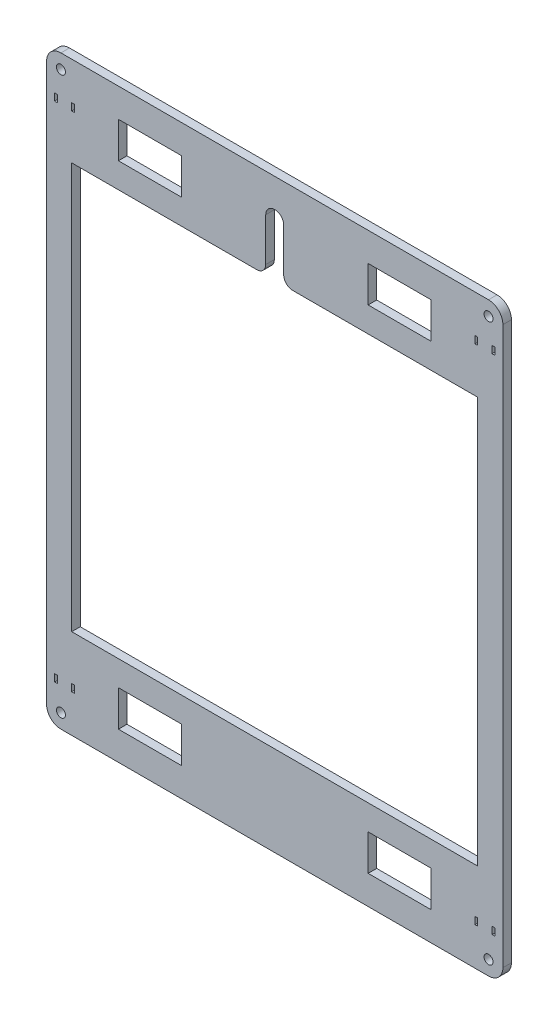
SolidWorks part; units mm, degrees
ref_plane "Front Plane" through (0, 0, 0) normal (0, 0, 1) x (1, 0, 0)
ref_plane "Top Plane" through (0, 0, 0) normal (0, 1, 0) x (1, 0, 0)
ref_plane "Right Plane" through (0, 0, 0) normal (1, 0, 0) x (0, 0, -1)
sketch "Sketch1" plane through (0, 0, 0) normal (0, 0, 1) x (1, 0, 0)
  line L4 (-66.9426, 67.8064) -> (-66.9426, -242.1936)
  line L5 (-58.9426, -250.1936) -> (179.0574, -250.1936)
  line L6 (187.0574, -242.1936) -> (187.0574, 67.8064)
  line L7 (179.0574, 75.8064) -> (-58.9426, 75.8064)
  line L8 (-66.9426, 67.8064) -> (-66.9426, -242.1936)
  line L9 (-58.9426, -250.1936) -> (179.0574, -250.1936)
  line L10 (187.0574, -242.1936) -> (187.0574, 67.8064)
  line L11 (179.0574, 75.8064) -> (-58.9426, 75.8064)
  arc A4 (-66.9426, -242.1936) -> (-58.9426, -250.1936) centre (-58.9426, -242.1936) ccw
  arc A5 (179.0574, -250.1936) -> (187.0574, -242.1936) centre (179.0574, -242.1936) ccw
  arc A6 (187.0574, 67.8064) -> (179.0574, 75.8064) centre (179.0574, 67.8064) ccw
  arc A7 (-58.9426, 75.8064) -> (-66.9426, 67.8064) centre (-58.9426, 67.8064) ccw
  arc A8 (-66.9426, -242.1936) -> (-58.9426, -250.1936) centre (-58.9426, -242.1936) ccw
  arc A9 (179.0574, -250.1936) -> (187.0574, -242.1936) centre (179.0574, -242.1936) ccw
  arc A10 (187.0574, 67.8064) -> (179.0574, 75.8064) centre (179.0574, 67.8064) ccw
  arc A11 (-58.9426, 75.8064) -> (-66.9426, 67.8064) centre (-58.9426, 67.8064) ccw
  dimension "D1" = 0
extrude "Boss-Extrude1" add sketch "Sketch1" against normal blind 4.7625 contours L9 A9 L10 A10 L11 A11 L8 A8
sketch "Sketch2" plane through (0, 0, 0) normal (0, 0, 1) x (1, 0, 0)
  line L0 (-66.9426, -87.1936) -> (187.0574, -87.1936) construction
  line L1 (-66.9426, 67.8064) -> (-66.9426, -242.1936) construction
  line L2 (187.0574, -242.1936) -> (187.0574, 67.8064) construction
  line L3 (60.0574, 75.8064) -> (60.0574, -250.1936) construction
  line L4 (179.0574, 75.8064) -> (-58.9426, 75.8064) construction
  line L5 (-58.9426, -250.1936) -> (179.0574, -250.1936) construction
  line L14 (173.0574, 25.8064) -> (70.0574, 25.8064)
  line L15 (173.0574, -200.1936) -> (173.0574, 25.8064)
  line L16 (-52.9426, -200.1936) -> (173.0574, -200.1936)
  line L17 (-52.9426, 25.8064) -> (-52.9426, -200.1936)
  line L18 (50.0574, 25.8064) -> (-52.9426, 25.8064)
  line L19 (55.0574, 54.8064) -> (55.0574, 30.8064)
  line L20 (65.0574, 30.8064) -> (65.0574, 54.8064)
  line L22 (8.0574, 39.8064) -> (8.0574, 59.8064)
  line L23 (-26.9426, 39.8064) -> (8.0574, 39.8064)
  line L24 (-26.9426, 59.8064) -> (-26.9426, 39.8064)
  line L25 (8.0574, 59.8064) -> (-26.9426, 59.8064)
  line L30 (147.0574, 59.8064) -> (112.0574, 59.8064)
  line L31 (147.0574, 39.8064) -> (147.0574, 59.8064)
  line L32 (112.0574, 39.8064) -> (147.0574, 39.8064)
  line L33 (112.0574, 59.8064) -> (112.0574, 39.8064)
  line L38 (-62.4426, 50.8064) -> (-60.9426, 50.8064)
  line L39 (-62.4426, 54.8064) -> (-62.4426, 50.8064)
  line L40 (-60.9426, 54.8064) -> (-62.4426, 54.8064)
  line L41 (-60.9426, 50.8064) -> (-60.9426, 54.8064)
  line L46 (-52.9426, 50.8064) -> (-51.4426, 50.8064)
  line L47 (-52.9426, 54.8064) -> (-52.9426, 50.8064)
  line L48 (-51.4426, 54.8064) -> (-52.9426, 54.8064)
  line L49 (-51.4426, 50.8064) -> (-51.4426, 54.8064)
  line L54 (173.0574, 54.8064) -> (171.5574, 54.8064)
  line L55 (173.0574, 50.8064) -> (173.0574, 54.8064)
  line L56 (171.5574, 50.8064) -> (173.0574, 50.8064)
  line L57 (171.5574, 54.8064) -> (171.5574, 50.8064)
  line L62 (182.5574, 54.8064) -> (181.0574, 54.8064)
  line L63 (182.5574, 50.8064) -> (182.5574, 54.8064)
  line L64 (181.0574, 50.8064) -> (182.5574, 50.8064)
  line L65 (181.0574, 54.8064) -> (181.0574, 50.8064)
  line L70 (-26.9426, -234.1936) -> (8.0574, -234.1936)
  line L71 (-26.9426, -214.1936) -> (-26.9426, -234.1936)
  line L72 (8.0574, -214.1936) -> (-26.9426, -214.1936)
  line L73 (8.0574, -234.1936) -> (8.0574, -214.1936)
  line L78 (-62.4426, -229.1936) -> (-60.9426, -229.1936)
  line L79 (-62.4426, -225.1936) -> (-62.4426, -229.1936)
  line L80 (-60.9426, -225.1936) -> (-62.4426, -225.1936)
  line L81 (-60.9426, -229.1936) -> (-60.9426, -225.1936)
  line L86 (-52.9426, -229.1936) -> (-51.4426, -229.1936)
  line L87 (-52.9426, -225.1936) -> (-52.9426, -229.1936)
  line L88 (-51.4426, -225.1936) -> (-52.9426, -225.1936)
  line L89 (-51.4426, -229.1936) -> (-51.4426, -225.1936)
  line L94 (182.5574, -225.1936) -> (181.0574, -225.1936)
  line L95 (182.5574, -229.1936) -> (182.5574, -225.1936)
  line L96 (181.0574, -229.1936) -> (182.5574, -229.1936)
  line L97 (181.0574, -225.1936) -> (181.0574, -229.1936)
  line L102 (173.0574, -225.1936) -> (171.5574, -225.1936)
  line L103 (173.0574, -229.1936) -> (173.0574, -225.1936)
  line L104 (171.5574, -229.1936) -> (173.0574, -229.1936)
  line L105 (171.5574, -225.1936) -> (171.5574, -229.1936)
  line L110 (112.0574, -214.1936) -> (112.0574, -234.1936)
  line L111 (147.0574, -214.1936) -> (112.0574, -214.1936)
  line L112 (147.0574, -234.1936) -> (147.0574, -214.1936)
  line L113 (112.0574, -234.1936) -> (147.0574, -234.1936)
  circle A2 centre (179.0574, 67.8064) radius 2.5
  arc A6 (65.0574, 30.8064) -> (70.0574, 25.8064) centre (70.0574, 30.8064) ccw
  arc A7 (50.0574, 25.8064) -> (55.0574, 30.8064) centre (50.0574, 30.8064) ccw
  arc A8 (65.0574, 54.8064) -> (55.0574, 54.8064) centre (60.0574, 54.8064) ccw
  circle A10 centre (-58.9426, 67.8064) radius 2.5
  circle A12 centre (-58.9426, -242.1936) radius 2.5
  circle A14 centre (179.0574, -242.1936) radius 2.5
  dimension "D6" = 5
  dimension "D10" = 29
  dimension "D11" = 5
  dimension "D19" = 119
  dimension "D1" = 226
  dimension "D2" = 113
  dimension "D3" = 127
  dimension "D4" = 127
  dimension "D5" = 138
  dimension "D7" = 238
  dimension "D8" = 155
  dimension "D9" = 119
  dimension "D12" = 35
  dimension "D13" = 52
  dimension "D14" = 52
  dimension "D15" = 8
  dimension "D16" = 111.5
  dimension "D17" = 8
  dimension "D18" = 25
  dimension "D20" = 310
extrude "Cut-Extrude1" cut sketch "Sketch2" against normal blind 10
